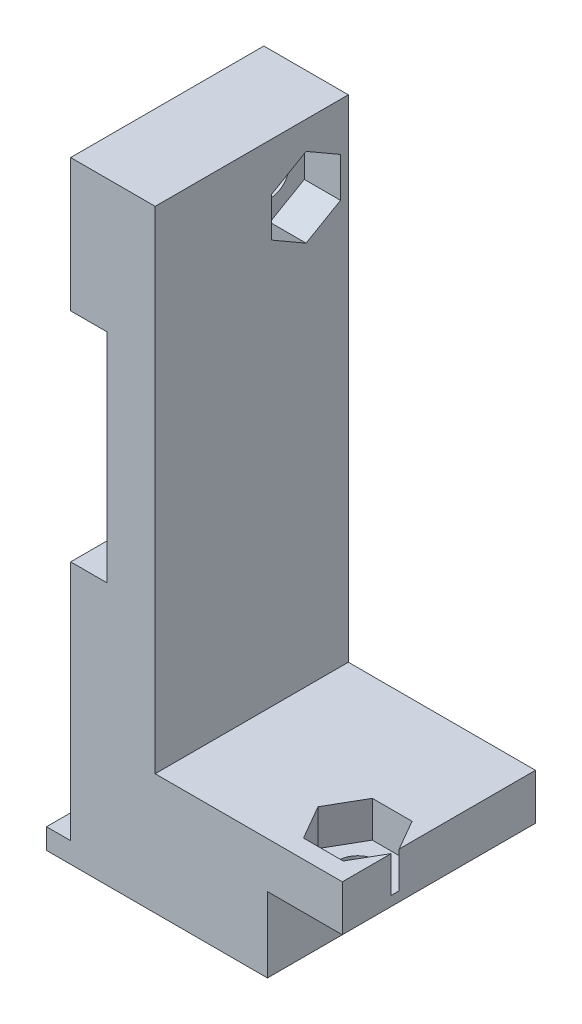
SolidWorks part; units mm, degrees
ref_plane "Alzado" through (0, 0, 0) normal (0, 0, 1) x (1, 0, 0)
ref_plane "Planta" through (0, 0, 0) normal (0, 1, 0) x (1, 0, 0)
ref_plane "Vista lateral" through (0, 0, 0) normal (1, 0, 0) x (0, 0, -1)
sketch "Croquis1" plane through (0, 0, 0) normal (0, 0, 1) x (1, 0, 0)
  line L0 (0, 0) -> (0, 1.7)
  line L1 (0, 1.7) -> (2, 1.7)
  line L2 (2, 1.7) -> (2, 21.7)
  line L3 (2, 21.7) -> (5, 21.7)
  line L4 (5, 21.7) -> (5, 39.7)
  line L5 (5, 39.7) -> (2, 39.7)
  line L6 (2, 39.7) -> (2, 50.7)
  line L7 (2, 50.7) -> (9, 50.7)
  line L8 (9, 50.7) -> (9, 10)
  line L10 (9, 10) -> (24.5, 10)
  line L11 (24.5, 10) -> (24.5, 0)
  line L12 (24.5, 0) -> (0, 0)
  dimension "D1" = 1.7
  dimension "D2" = 22.5
  dimension "D3" = 2
  dimension "D4" = 20
  dimension "D5" = 49
  dimension "D6" = 18
  dimension "D7" = 3
  dimension "D8" = 7
  dimension "D9" = 10
extrude "Saliente-Extruir1" add sketch "Croquis1" along normal blind 16
sketch "Croquis2" plane through (0, 0, 16) normal (0, 0, 1) x (1, 0, 0)
  line L1 (24.5, 0) -> (18.3, 0)
  line L2 (24.5, 0) -> (24.5, 6.2)
  line L3 (24.5, 6.2) -> (18.3, 6.2)
  line L4 (18.3, 0) -> (18.3, 6.2)
  dimension "D1" = 6.2
extrude "Cortar-Extruir1" cut sketch "Croquis2" against normal up to next
sketch "Croquis3" plane through (2, 0, 0) normal (-1, 0, 0) x (0, 0, 1)
  line L0 (0, 50.7) -> (0, 39.7) construction
  line L1 (16, 1.7) -> (0, 1.7) construction
  circle A0 centre (3.5, 45.1) radius 1.6
  dimension "D2" = 3.2
  dimension "D1" = 3.5
  dimension "D3" = 43.4
extrude "Cortar-Extruir2" cut sketch "Croquis3" against normal up to next
sketch "Croquis4" plane through (9, 0, 0) normal (1, 0, 0) x (0, 0, -1)
  line L1 (-0.65, 46.7454) -> (-3.5, 48.3909)
  line L2 (-3.5, 48.3909) -> (-6.35, 46.7454)
  line L3 (-6.35, 46.7454) -> (-6.35, 43.4546)
  line L4 (-6.35, 43.4546) -> (-3.5, 41.8091)
  line L5 (-3.5, 41.8091) -> (-0.65, 43.4546)
  line L6 (-0.65, 43.4546) -> (-0.65, 46.7454)
  circle A0 centre (-3.5, 45.1) radius 2.85 construction
  dimension "D1" = 5.7
extrude "Cortar-Extruir3" cut sketch "Croquis4" against normal blind 3
sketch "Croquis5" plane through (0, 6.2, 0) normal (0, -1, 0) x (1, 0, 0)
  line L0 (24.5, 0) -> (18.3, 0) construction
  line L1 (24.5, 0) -> (24.5, 16) construction
  circle A0 centre (21.4, 11.62) radius 1.6
  dimension "D1" = 3.2
  dimension "D2" = 11.62
  dimension "D3" = 3.1
extrude "Cortar-Extruir4" cut sketch "Croquis5" against normal up to next
sketch "Croquis6" plane through (0, 10, 0) normal (0, 1, 0) x (1, 0, 0)
  line L1 (19.7546, -14.47) -> (23.0454, -14.47)
  line L2 (23.0454, -14.47) -> (24.6909, -11.62)
  line L3 (24.6909, -11.62) -> (23.0454, -8.77)
  line L4 (23.0454, -8.77) -> (19.7546, -8.77)
  line L5 (19.7546, -8.77) -> (18.1091, -11.62)
  line L6 (18.1091, -11.62) -> (19.7546, -14.47)
  circle A0 centre (21.4, -11.62) radius 2.85 construction
  dimension "D1" = 5.7
extrude "Cortar-Extruir5" cut sketch "Croquis6" against normal blind 3
